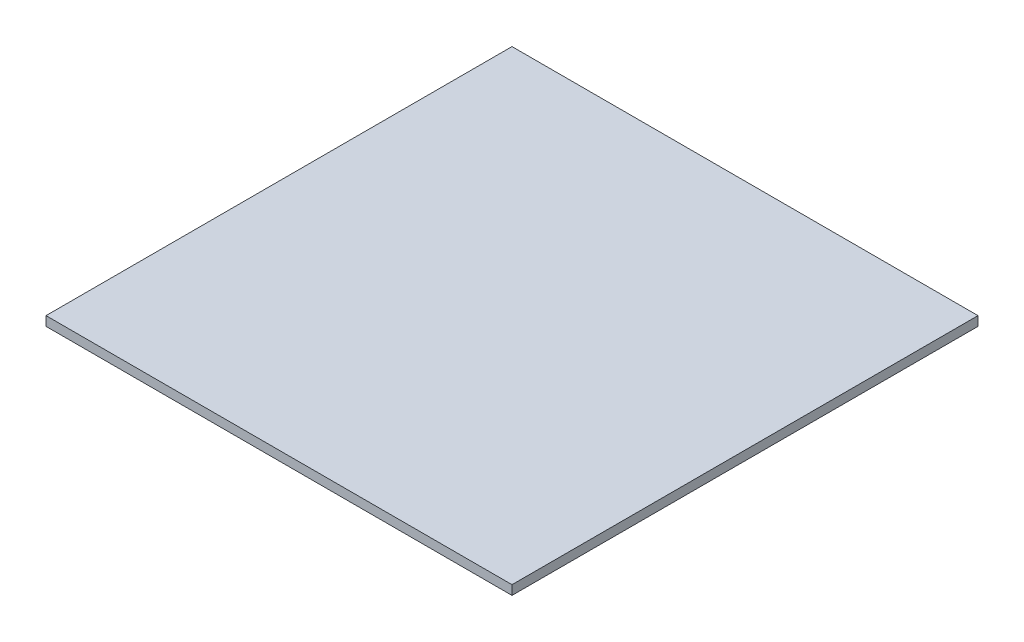
SolidWorks part; units mm, degrees
ref_plane "Front Plane" through (0, 0, 0) normal (0, 0, 1) x (1, 0, 0)
ref_plane "Top Plane" through (0, 0, 0) normal (0, 1, 0) x (1, 0, 0)
ref_plane "Right Plane" through (0, 0, 0) normal (1, 0, 0) x (0, 0, -1)
sketch "Sketch1" plane through (0, 0, 0) normal (0, 1, 0) x (1, 0, 0)
  line L1 (0, 0) -> (200, 0)
  line L2 (0, 0) -> (0, 200)
  line L3 (0, 200) -> (200, 200)
  line L4 (200, 0) -> (200, 200)
  dimension "D1" = 200
extrude "Boss-Extrude1" add sketch "Sketch1" along normal blind 4
